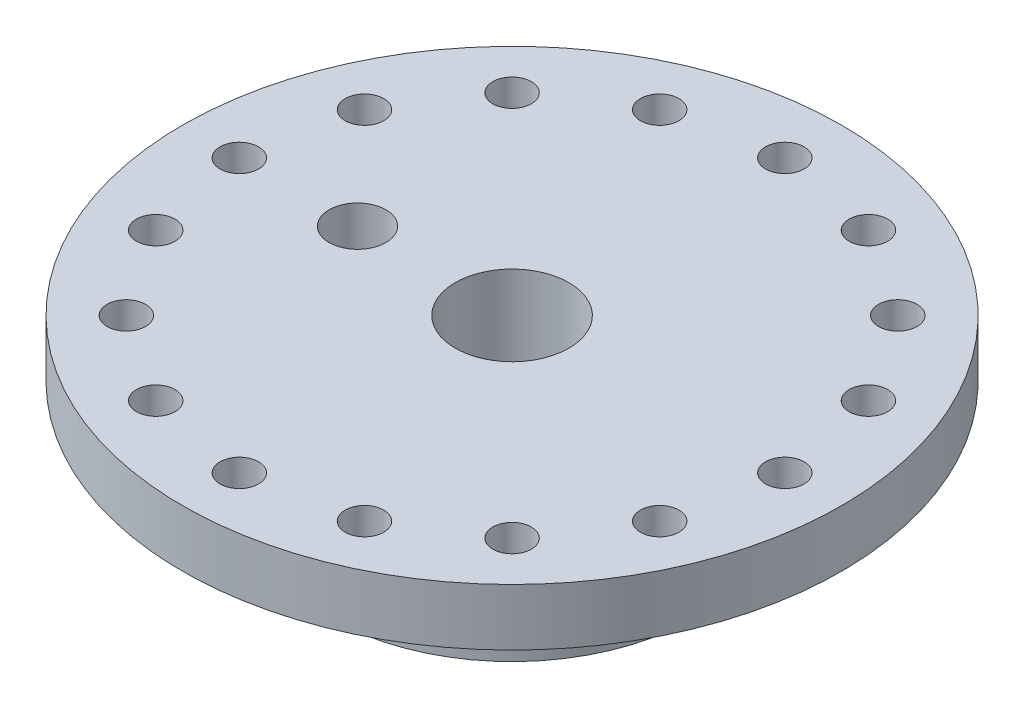
SolidWorks part; units mm, degrees
material "AISI 316 Annealed Stainless Steel Bar (SS)"
ref_plane "Front Plane" through (0, 0, 0) normal (0, 0, 1) x (1, 0, 0)
ref_plane "Top Plane" through (0, 0, 0) normal (0, 1, 0) x (1, 0, 0)
ref_plane "Right Plane" through (0, 0, 0) normal (1, 0, 0) x (0, 0, -1)
sketch "Sketch1" plane through (0, 0, 0) normal (0, 0, 1) x (1, 0, 0)
  line L10 (-36.83, 19.05) -> (-6.35, 19.05)
  line L17 (-6.35, 19.05) -> (-6.35, 0)
  line L18 (-6.35, 0) -> (-20.447, 0)
  line L19 (-20.447, 0) -> (-20.447, 6.35)
  line L20 (-20.447, 6.35) -> (-14.097, 6.35)
  line L21 (-14.097, 6.35) -> (-14.097, 12.7)
  line L22 (-14.097, 12.7) -> (-36.83, 12.7)
  line L23 (-36.83, 12.7) -> (-36.83, 19.05)
  line L24 (0, 0) -> (0, 18.8903) construction
  dimension "D1" = 40.894
  dimension "D2" = 6.35
  dimension "D3" = 6.35
  dimension "D4" = 6.35
  dimension "D5" = 6.35
  dimension "D6" = 73.66
  dimension "D7" = 12.7
revolve "Revolve1" add sketch "Sketch1" angle 360 about L24
sketch "Sketch2" plane through (0, 19.05, 0) normal (0, 1, 0) x (1, 0, 0)
  line L0 (0, 30.48) -> (0, 0) construction
  line L1 (-17.272, 0) -> (0, 0) construction
  circle A0 centre (0, 30.48) radius 2.1526
  circle A1 centre (11.6642, 28.1598) radius 2.1526
  circle A2 centre (21.5526, 21.5526) radius 2.1527
  circle A3 centre (28.1598, 11.6642) radius 2.1527
  circle A4 centre (30.48, 0) radius 2.1527
  circle A5 centre (28.1598, -11.6642) radius 2.1527
  circle A6 centre (21.5526, -21.5526) radius 2.1527
  circle A7 centre (11.6642, -28.1598) radius 2.1527
  circle A8 centre (0, -30.48) radius 2.1527
  circle A9 centre (-11.6642, -28.1598) radius 2.1527
  circle A10 centre (-21.5526, -21.5526) radius 2.1527
  circle A11 centre (-28.1598, -11.6642) radius 2.1527
  circle A12 centre (-30.48, 0) radius 2.1527
  circle A13 centre (-28.1598, 11.6642) radius 2.1527
  circle A14 centre (-21.5526, 21.5526) radius 2.1527
  circle A15 centre (-11.6642, 28.1598) radius 2.1527
  circle A16 centre (-17.272, 0) radius 3.175
  point P37 (0, 0)
  dimension "D2" = 4.3053
  dimension "D5" = 6.35
  dimension "D1" = 30.48
  dimension "D4" = 17.272
  dimension "D3" = 16
extrude "Cut-Extrude1" cut sketch "Sketch2" against normal up to next
sketch "Sketch3" plane through (0, 0, 0) normal (0, -1, 0) x (1, 0, 0)
  line L0 (0, 16.51) -> (0, 0) construction
  circle A0 centre (0, 16.51) radius 0.3969
  circle A1 centre (3.2209, 16.1928) radius 0.3969
  circle A2 centre (6.3181, 15.2533) radius 0.3969
  circle A3 centre (9.1725, 13.7276) radius 0.3969
  circle A4 centre (11.6743, 11.6743) radius 0.3969
  circle A5 centre (13.7276, 9.1725) radius 0.3969
  circle A6 centre (15.2533, 6.3181) radius 0.3969
  circle A7 centre (16.1928, 3.2209) radius 0.3969
  circle A8 centre (16.51, 0) radius 0.3969
  circle A9 centre (16.1928, -3.2209) radius 0.3969
  circle A10 centre (15.2533, -6.3181) radius 0.3969
  circle A11 centre (13.7276, -9.1725) radius 0.3969
  circle A12 centre (11.6743, -11.6743) radius 0.3969
  circle A13 centre (9.1725, -13.7276) radius 0.3969
  circle A14 centre (6.3181, -15.2533) radius 0.3969
  circle A15 centre (3.2209, -16.1928) radius 0.3969
  circle A16 centre (0, -16.51) radius 0.3969
  circle A17 centre (-3.2209, -16.1928) radius 0.3969
  circle A18 centre (-6.3181, -15.2533) radius 0.3969
  circle A19 centre (-9.1725, -13.7276) radius 0.3969
  circle A20 centre (-11.6743, -11.6743) radius 0.3969
  circle A21 centre (-13.7276, -9.1725) radius 0.3969
  circle A22 centre (-15.2533, -6.3181) radius 0.3969
  circle A23 centre (-16.1928, -3.2209) radius 0.3969
  circle A24 centre (-16.51, 0) radius 0.3969
  circle A25 centre (-16.1928, 3.2209) radius 0.3969
  circle A26 centre (-15.2533, 6.3181) radius 0.3969
  circle A27 centre (-13.7276, 9.1725) radius 0.3969
  circle A28 centre (-11.6743, 11.6743) radius 0.3969
  circle A29 centre (-9.1725, 13.7276) radius 0.3969
  circle A30 centre (-6.3181, 15.2533) radius 0.3969
  circle A31 centre (-3.2209, 16.1928) radius 0.3969
  point P69 (0, 0)
  dimension "D2" = 0.7937
  dimension "D1" = 16.51
  dimension "D3" = 32
extrude "Cut-Extrude2" cut sketch "Sketch3" against normal up to next (6.35 mm away)
